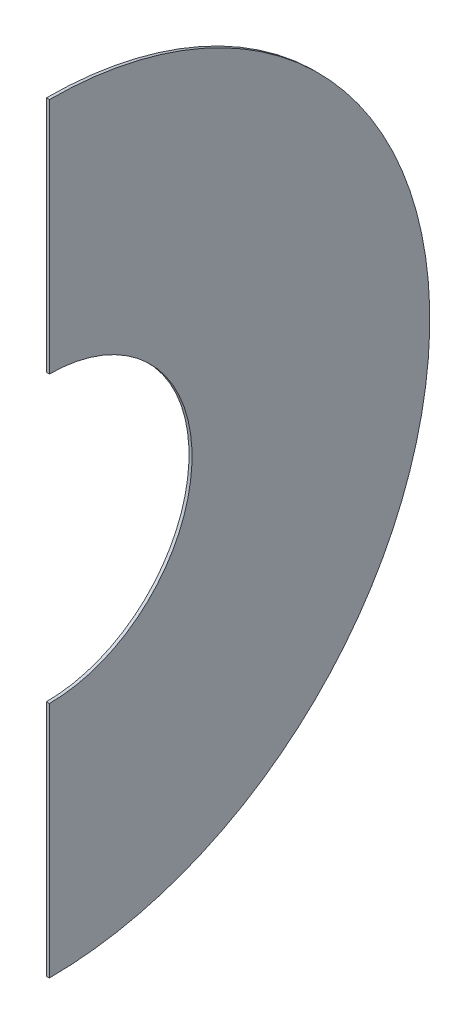
SolidWorks part; units mm, degrees
ref_plane "Front Plane" through (0, 0, 0) normal (0, 0, 1) x (1, 0, 0)
ref_plane "Top Plane" through (0, 0, 0) normal (0, 1, 0) x (1, 0, 0)
ref_plane "Right Plane" through (0, 0, 0) normal (1, 0, 0) x (0, 0, -1)
sketch "Sketch1" plane through (0, 0, 0) normal (1, 0, 0) x (0, 0, -1)
  line L0 (0, 200) -> (0, -200)
  circle A0 centre (0, 0) radius 200
  circle A1 centre (0, 0) radius 75
extrude "Boss-Extrude1" add sketch "Sketch1" along normal blind 1.5875 contours A1 L0 A0
